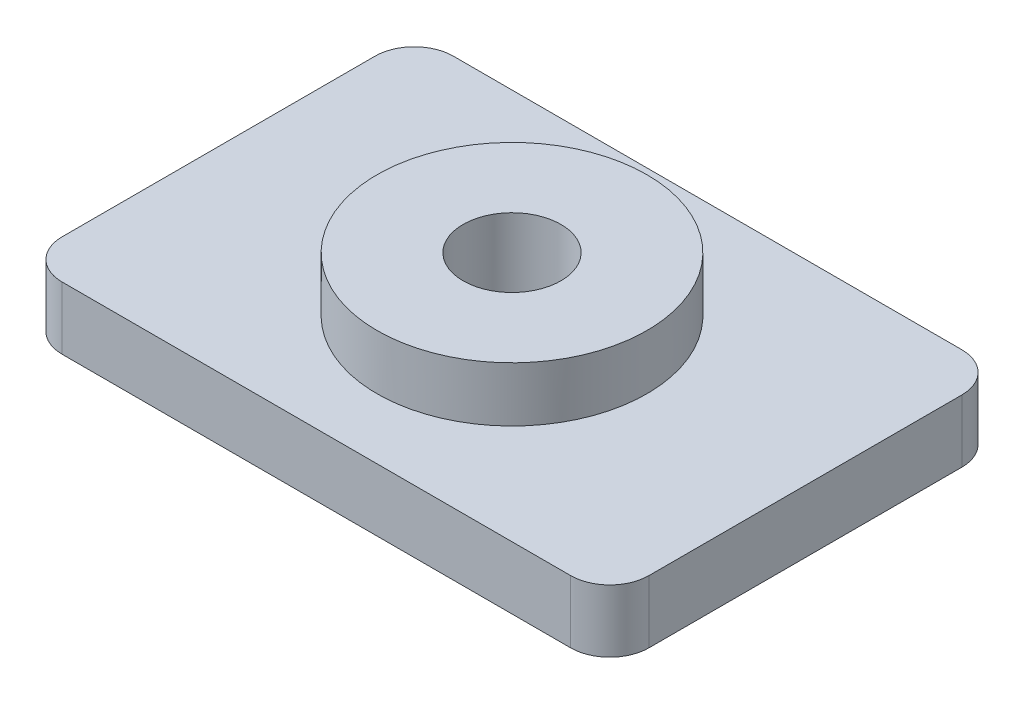
SolidWorks part; units mm, degrees
ref_plane "Alzado" through (0, 0, 0) normal (0, 0, 1) x (1, 0, 0)
ref_plane "Planta" through (0, 0, 0) normal (0, 1, 0) x (1, 0, 0)
ref_plane "Vista lateral" through (0, 0, 0) normal (1, 0, 0) x (0, 0, -1)
sketch "Croquis1" plane through (0, 0, 0) normal (0, 1, 0) x (1, 0, 0)
  line L1 (1, 0) -> (14, 0)
  line L2 (0, 1) -> (0, 9)
  line L3 (1, 10) -> (14, 10)
  line L4 (15, 1) -> (15, 9)
  arc A0 (14, 10) -> (15, 9) centre (14, 9) cw
  arc A1 (14, 0) -> (15, 1) centre (14, 1) ccw
  arc A2 (1, 0) -> (0, 1) centre (1, 1) cw
  arc A3 (0, 9) -> (1, 10) centre (1, 9) cw
  point P7 (15, 10)
  point P10 (15, 0)
  point P13 (0, 0)
  dimension "D3" = 1
  dimension "D1" = 10
  dimension "D2" = 15
extrude "Saliente-Extruir1" add sketch "Croquis1" along normal blind 1.6
sketch "Croquis2" plane through (0, 1.6, 0) normal (0, 1, 0) x (1, 0, 0)
  line L0 (0, 5) -> (15, 5) construction
  line L1 (0, 9) -> (0, 1) construction
  line L2 (15, 1) -> (15, 9) construction
  circle A0 centre (7.5, 5) radius 3.45
  dimension "D1" = 6.9
extrude "Saliente-Extruir2" add sketch "Croquis2" along normal blind 1.4
sketch "Croquis3" plane through (0, 3, 0) normal (0, 1, 0) x (1, 0, 0)
  circle A0 centre (7.5, 5) radius 1.25
  circle A1 centre (7.5, 5) radius 3.45 construction
  dimension "D1" = 2.5
extrude "Cortar-Extruir1" cut sketch "Croquis3" against normal up to next
